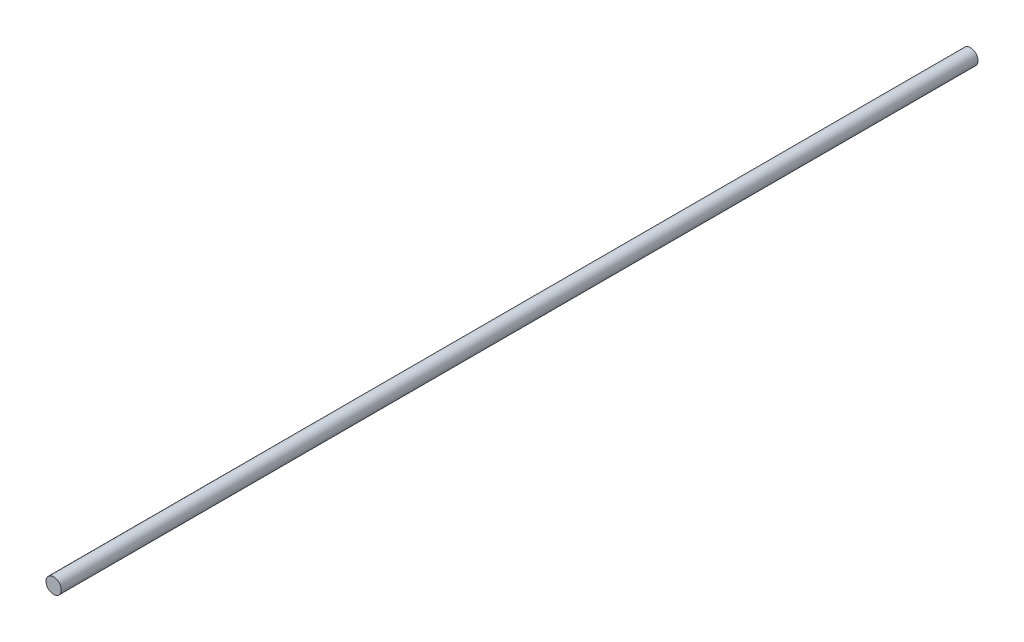
SolidWorks part; units mm, degrees
ref_plane "Front Plane" through (0, 0, 0) normal (0, 0, 1) x (1, 0, 0)
ref_plane "Top Plane" through (0, 0, 0) normal (0, 1, 0) x (1, 0, 0)
ref_plane "Right Plane" through (0, 0, 0) normal (1, 0, 0) x (0, 0, -1)
sketch "Sketch1" plane through (0, 0, 0) normal (0, 0, 1) x (1, 0, 0)
  circle A0 centre (0.1438, 0.9444) radius 2.5
  dimension "D1" = 5
extrude "Boss-Extrude1" add sketch "Sketch1" along normal blind 300
